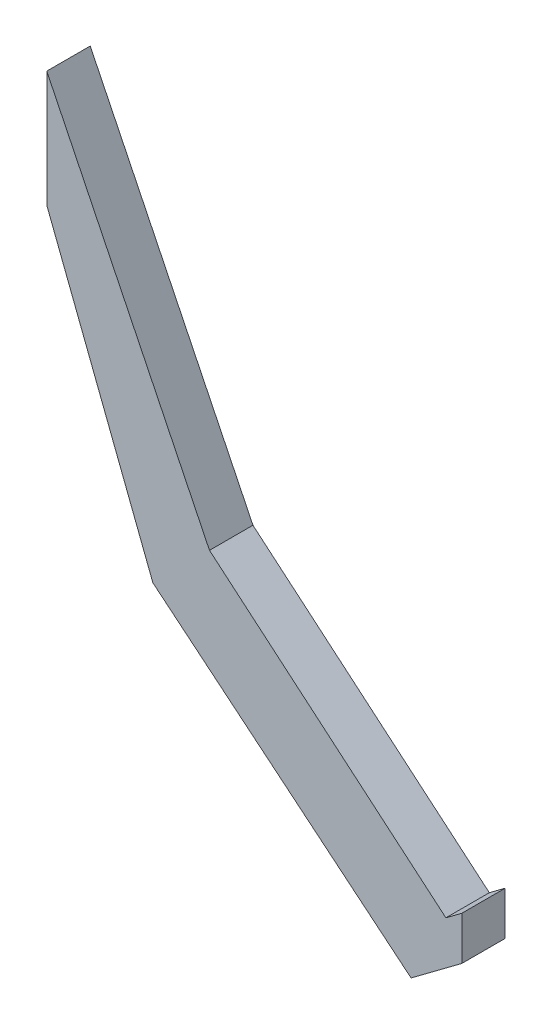
SolidWorks part; units mm, degrees
ref_plane "Alzado" through (0, 0, 0) normal (0, 0, 1) x (1, 0, 0)
ref_plane "Planta" through (0, 0, 0) normal (0, 1, 0) x (1, 0, 0)
ref_plane "Vista lateral" through (0, 0, 0) normal (1, 0, 0) x (0, 0, -1)
sketch "Croquis1" plane through (0, 0, 0) normal (0, 0, 1) x (1, 0, 0)
  line L1 (-2.5236, -23.0179) -> (-0.6939, -21.6496)
  line L2 (-0.6939, -21.6496) -> (-0.6939, -26.6561)
  line L3 (-0.6939, -26.6561) -> (-6.5291, -31.0198)
  line L5 (-48.4511, 25.0386) -> (-48.4511, 38.3968)
  line L6 (-48.4511, 25.0386) -> (-36.24, -6.4922)
  line L7 (-36.24, -6.4922) -> (-6.5291, -31.0198)
  line L8 (-48.4511, 38.3968) -> (-29.7265, 0)
  line L9 (-29.7265, 0) -> (-2.5236, -23.0179)
  dimension "D1" = 70
extrude "Saliente-Extruir1" add sketch "Croquis1" along normal blind 5
